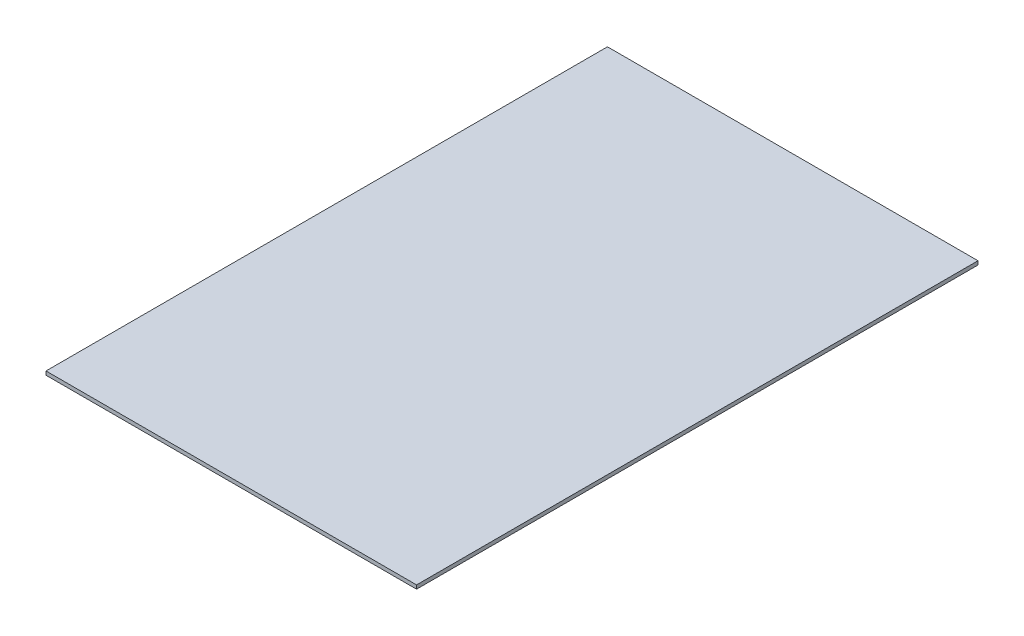
SolidWorks part; units mm, degrees
ref_plane "Front Plane" through (0, 0, 0) normal (0, 0, 1) x (1, 0, 0)
ref_plane "Top Plane" through (0, 0, 0) normal (0, 1, 0) x (1, 0, 0)
ref_plane "Right Plane" through (0, 0, 0) normal (1, 0, 0) x (0, 0, -1)
sketch "Sketch1" plane through (0, 0, 0) normal (0, 1, 0) x (1, 0, 0)
  line L1 (99, 150) -> (-99, 150)
  line L2 (99, 150) -> (99, -150)
  line L3 (99, -150) -> (-99, -150)
  line L4 (-99, 150) -> (-99, -150)
  line L5 (99, 150) -> (-99, -150) construction
  line L6 (99, -150) -> (-99, 150) construction
  point P0 (0, 0)
  dimension "D1" = 198
  dimension "D2" = 300
extrude "Boss-Extrude1" add sketch "Sketch1" along normal blind 2
